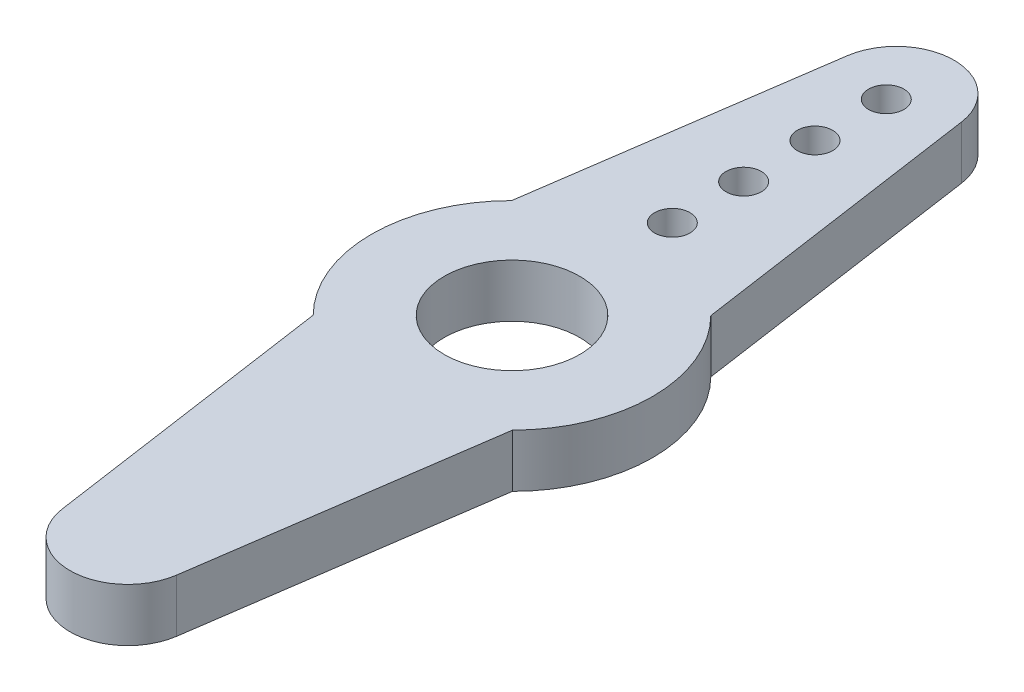
SolidWorks part; units mm, degrees
ref_plane "Front Plane" through (0, 0, 0) normal (0, 0, 1) x (1, 0, 0)
ref_plane "Top Plane" through (0, 0, 0) normal (0, 1, 0) x (1, 0, 0)
ref_plane "Right Plane" through (0, 0, 0) normal (1, 0, 0) x (0, 0, -1)
sketch "Sketch1" plane through (0, 0, 0) normal (0, 1, 0) x (1, 0, 0)
  line L0 (-4.2926, 4.2745) -> (-2.4665, 16.9142)
  line L1 (4.2926, 4.2745) -> (2.4665, 16.9142)
  line L2 (-4.2926, -4.2745) -> (-2.4665, -16.9142)
  line L3 (4.2926, -4.2745) -> (2.4665, -16.9142)
  line L4 (0, 19.05) -> (0, -19.05) construction
  circle A0 centre (0, 0) radius 2.921
  arc A1 (4.2926, -4.2745) -> (4.2926, 4.2745) centre (0, 0) ccw
  arc A2 (-2.4665, -16.9142) -> (2.4665, -16.9142) centre (0, -16.5579) ccw
  arc A3 (-2.4665, 16.9142) -> (2.4665, 16.9142) centre (0, 16.5579) cw
  arc A4 (-4.2926, 4.2745) -> (-4.2926, -4.2745) centre (0, 0) ccw
  circle A5 centre (0, 16.129) radius 0.762
  circle A6 centre (0, 13.0556) radius 0.762
  circle A7 centre (0, 9.9822) radius 0.762
  circle A8 centre (0, 6.9088) radius 0.762
  dimension "D1" = 5.842
  dimension "D2" = 12.1158
  dimension "D3" = 38.1
  dimension "D5" = 1.524
  dimension "D4" = 8.5852
  dimension "D6" = 6.9088
  dimension "D7" = 3.0734
  dimension "D8" = 3.0734
  dimension "D9" = 3.0734
extrude "Boss-Extrude1" add sketch "Sketch1" along normal blind 2.286
